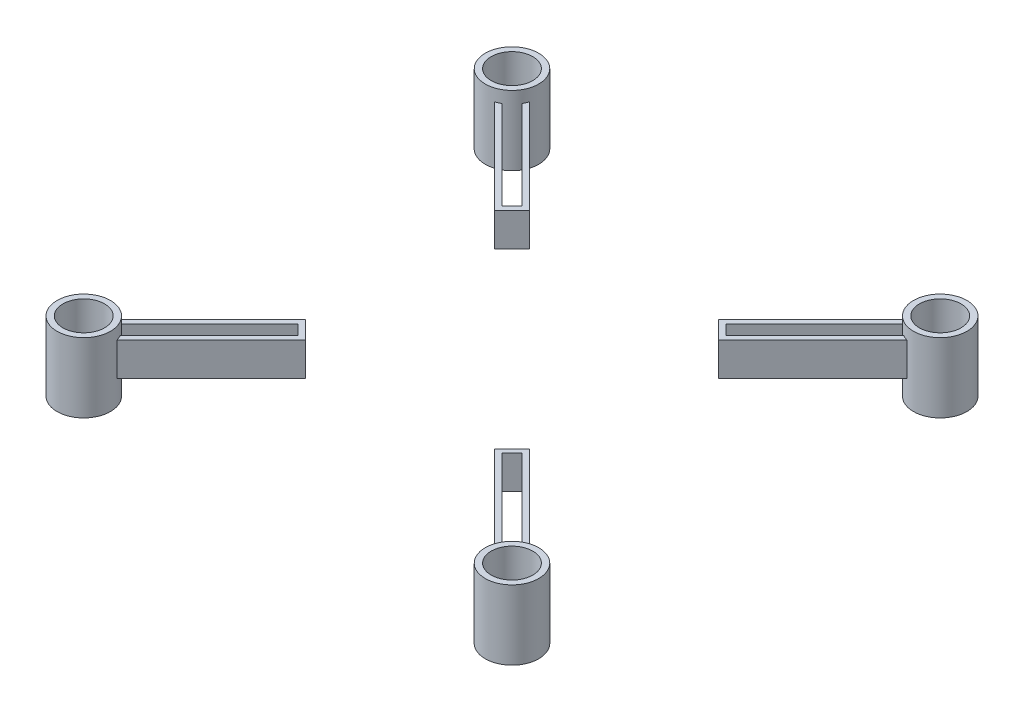
SolidWorks part; units mm, degrees
ref_plane "Front Plane" through (0, 0, 0) normal (0, 0, 1) x (1, 0, 0)
ref_plane "Top Plane" through (0, 0, 0) normal (0, 1, 0) x (1, 0, 0)
ref_plane "Right Plane" through (0, 0, 0) normal (1, 0, 0) x (0, 0, -1)
sketch "Sketch1" plane through (0, 0, 0) normal (0, 1, 0) x (1, 0, 0)
  line L0 (0, 0) -> (-35.0294, 0) construction
  line L1 (-30.445, -30.445) -> (0, 0) construction
  line L2 (0, 0) -> (0, -33.3699) construction
  circle A0 centre (-30.445, -30.445) radius 3.7999
  circle A1 centre (-30.445, -30.445) radius 2.96
  circle A2 centre (-30.445, 30.445) radius 2.96
  circle A3 centre (-30.445, 30.445) radius 3.7999
  circle A4 centre (30.445, 30.445) radius 2.96
  circle A5 centre (30.445, 30.445) radius 3.7999
  circle A6 centre (30.445, -30.445) radius 2.96
  circle A7 centre (30.445, -30.445) radius 3.7999
  point P20 (0, 0)
  dimension "D1" = 4
extrude "Boss-Extrude1" add sketch "Sketch1" along normal blind 9.89
ref_plane "Plane1" through (0, 8.18, 0) normal (0, 1, 0) x (1, 0, 0)
sketch "Sketch2" plane through (0, 8.18, 0) normal (0, 1, 0) x (1, 0, 0)
  line L0 (0, 0) -> (-27.7581, 27.7581) construction
  line L1 (-26.8158, 29.319) -> (-13.4268, 15.93)
  line L2 (-27.1355, 28.578) -> (-14.4875, 15.93)
  line L3 (-29.319, 26.8158) -> (-15.93, 13.4268)
  line L4 (-28.578, 27.1355) -> (-15.93, 14.4875)
  line L5 (0, 0) -> (-30.445, 30.445) construction
  line L6 (-15.93, 13.4268) -> (-13.4268, 15.93)
  line L7 (-15.93, 14.4875) -> (-14.4875, 15.93)
  line L8 (29.319, 26.8158) -> (15.93, 13.4268)
  line L9 (28.578, 27.1355) -> (15.93, 14.4875)
  line L10 (26.8158, 29.319) -> (13.4268, 15.93)
  line L11 (27.1355, 28.578) -> (14.4875, 15.93)
  line L12 (13.4268, 15.93) -> (15.93, 13.4268)
  line L13 (14.4875, 15.93) -> (15.93, 14.4875)
  line L14 (26.8158, -29.319) -> (13.4268, -15.93)
  line L15 (27.1355, -28.578) -> (14.4875, -15.93)
  line L16 (29.319, -26.8158) -> (15.93, -13.4268)
  line L17 (28.578, -27.1355) -> (15.93, -14.4875)
  line L18 (15.93, -13.4268) -> (13.4268, -15.93)
  line L19 (15.93, -14.4875) -> (14.4875, -15.93)
  line L20 (-29.319, -26.8158) -> (-15.93, -13.4268)
  line L21 (-28.578, -27.1355) -> (-15.93, -14.4875)
  line L22 (-26.8158, -29.319) -> (-13.4268, -15.93)
  line L23 (-27.1355, -28.578) -> (-14.4875, -15.93)
  line L24 (-13.4268, -15.93) -> (-15.93, -13.4268)
  line L25 (-14.4875, -15.93) -> (-15.93, -14.4875)
  circle A0 centre (-30.445, 30.445) radius 3.7999 construction
  arc A1 (-27.1355, 28.578) -> (-26.8158, 29.319) centre (-30.445, 30.445) ccw
  arc A2 (-29.319, 26.8158) -> (-28.578, 27.1355) centre (-30.445, 30.445) ccw
  arc A3 (28.578, 27.1355) -> (29.319, 26.8158) centre (30.445, 30.445) ccw
  arc A4 (26.8158, 29.319) -> (27.1355, 28.578) centre (30.445, 30.445) ccw
  arc A5 (27.1355, -28.578) -> (26.8158, -29.319) centre (30.445, -30.445) ccw
  arc A6 (29.319, -26.8158) -> (28.578, -27.1355) centre (30.445, -30.445) ccw
  arc A7 (-28.578, -27.1355) -> (-29.319, -26.8158) centre (-30.445, -30.445) ccw
  arc A8 (-26.8158, -29.319) -> (-27.1355, -28.578) centre (-30.445, -30.445) ccw
  point P44 (0, 0)
  dimension "D1" = 1.77
  dimension "D2" = 0.75
  dimension "D3" = 0.75
  dimension "D4" = 4
extrude "Boss-Extrude2" add sketch "Sketch2" against normal blind 4.74
